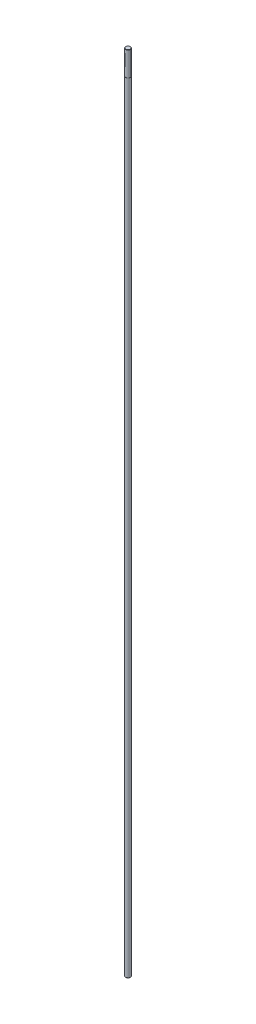
SolidWorks part; units mm, degrees
ref_plane "Front Plane" through (0, 0, 0) normal (0, 0, 1) x (1, 0, 0)
ref_plane "Top Plane" through (0, 0, 0) normal (0, 1, 0) x (1, 0, 0)
ref_plane "Right Plane" through (0, 0, 0) normal (1, 0, 0) x (0, 0, -1)
sketch "Sketch1" plane through (0, 0, 0) normal (0, 1, 0) x (1, 0, 0)
  circle A0 centre (0, 0) radius 2.1333
  dimension "D1" = 4.2667
extrude "Boss-Extrude1" add sketch "Sketch1" along normal blind 640 contours A0
sketch "Sketch2" plane through (0, 640, 0) normal (0, 1, 0) x (1, 0, 0)
  circle A0 centre (0, 0) radius 2
  dimension "D1" = 4
extrude "Boss-Extrude2" add sketch "Sketch2" along normal blind 20
chamfer "Chamfer1" distance 0.2 angle 45 1 edges at (0, 660, 2)
chamfer "Chamfer2" distance 0.5 angle 45 1 edges at (0, 0, 2.1333)
scale "Scale1" scale about centroid uniform scaling yes scale factor 7.5
